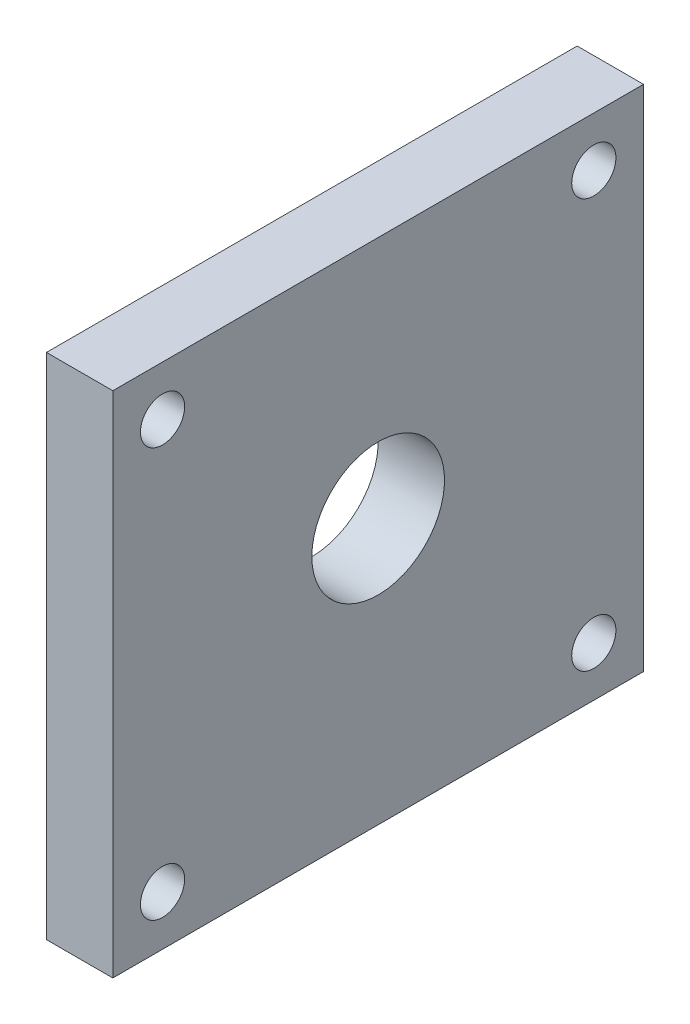
SolidWorks part; units mm, degrees
material "7079 Alloy"
ref_plane "Front Plane" through (0, 0, 0) normal (0, 0, 1) x (1, 0, 0)
ref_plane "Top Plane" through (0, 0, 0) normal (0, 1, 0) x (1, 0, 0)
ref_plane "Right Plane" through (0, 0, 0) normal (1, 0, 0) x (0, 0, -1)
sketch "Sketch1" plane through (0, 0, 0) normal (1, 0, 0) x (0, 0, -1)
  line L1 (0, 0) -> (76.2, 0)
  line L2 (0, 0) -> (0, -73.025)
  line L3 (0, -73.025) -> (76.2, -73.025)
  line L4 (76.2, 0) -> (76.2, -73.025)
  dimension "D1" = 76.2
  dimension "D2" = 73.025
extrude "Extrude1" add sketch "Sketch1" along normal blind 9.525
sketch "Sketch8" plane through (0, 0, 0) normal (-1, 0, 0) x (0, 0, 1)
  circle A1 centre (-7.1374, -7.1374) radius 3.175
  circle A2 centre (-69.0626, -7.1374) radius 3.175
  circle A3 centre (-69.0626, -65.8876) radius 3.175
  circle A4 centre (-7.1374, -65.8876) radius 3.175
  circle A5 centre (-38.1, -34.925) radius 9.525
  dimension "D1" = 6.35
  dimension "D2" = 6.35
  dimension "D3" = 6.35
  dimension "D5" = 6.35
  dimension "D8" = 19.05
extrude "Cut-Extrude5" cut sketch "Sketch8" against normal through all
